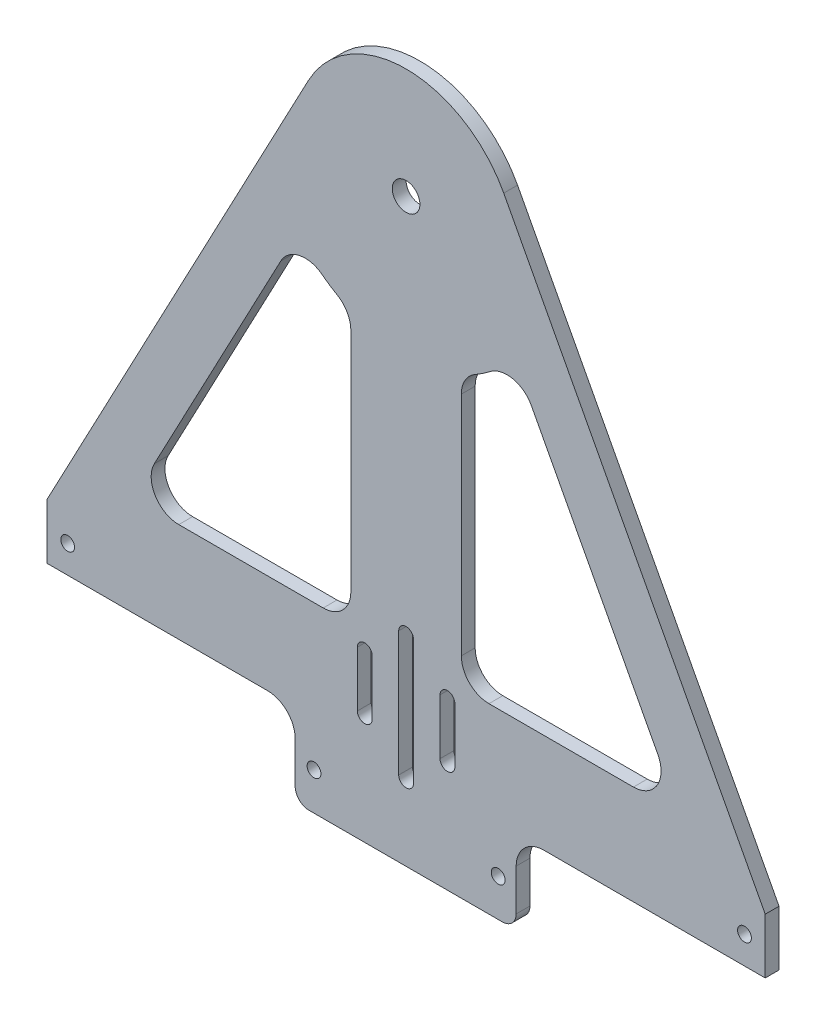
SolidWorks part; units mm, degrees
material "Hexcel AS4C (3000 Filaments)"
ref_plane "Front Plane" through (0, 0, 0) normal (0, 0, 1) x (1, 0, 0)
ref_plane "Top Plane" through (0, 0, 0) normal (0, 1, 0) x (1, 0, 0)
ref_plane "Right Plane" through (0, 0, 0) normal (1, 0, 0) x (0, 0, -1)
sketch "Sketch1" plane through (0, 0, 0) normal (0, 0, 1) x (1, 0, 0)
  line L0 (0, -58.42) -> (0, 58.42) construction
  line L2 (-82.55, 55.7897) -> (-82.55, -52.07)
  line L3 (-76.2, -58.42) -> (76.2, -58.42)
  line L4 (82.55, 55.7897) -> (82.55, -52.07)
  line L5 (-82.55, 58.42) -> (82.55, -58.42) construction
  line L6 (-82.55, -58.42) -> (82.55, 58.42) construction
  line L7 (-80.6901, 60.2799) -> (-75.4296, 65.5404)
  line L8 (-70.9395, 67.4003) -> (-50.8, 67.4003)
  line L9 (-46.3099, 65.5404) -> (-41.0494, 60.2799)
  line L10 (46.3099, 65.5404) -> (41.0494, 60.2799)
  line L11 (70.9395, 67.4003) -> (50.8, 67.4003)
  line L12 (80.6901, 60.2799) -> (75.4296, 65.5404)
  line L13 (-73.5697, 67.4003) -> (-82.55, 67.4003) construction
  line L14 (-82.55, 67.4003) -> (-82.55, 58.42) construction
  line L15 (-36.5592, 58.42) -> (0, 58.42)
  line L16 (0, 58.42) -> (36.5592, 58.42)
  circle A0 centre (-77.7875, -35.052) radius 1.5875
  circle A1 centre (-77.7875, -11.684) radius 1.5875
  circle A2 centre (-77.7875, 11.684) radius 1.5875
  circle A3 centre (-77.7875, 35.052) radius 1.5875
  circle A4 centre (77.7875, 35.052) radius 1.5875
  circle A5 centre (77.7875, 11.684) radius 1.5875
  circle A6 centre (77.7875, -11.684) radius 1.5875
  circle A7 centre (77.7875, -35.052) radius 1.5875
  arc A8 (82.55, 55.7897) -> (80.6901, 60.2799) centre (76.2, 55.7897) ccw
  arc A9 (75.4296, 65.5404) -> (70.9395, 67.4003) centre (70.9395, 61.0503) ccw
  arc A10 (46.3099, 65.5404) -> (50.8, 67.4003) centre (50.8, 61.0503) cw
  arc A11 (41.0494, 60.2799) -> (36.5592, 58.42) centre (36.5592, 64.77) cw
  arc A12 (-36.5592, 58.42) -> (-41.0494, 60.2799) centre (-36.5592, 64.77) cw
  arc A13 (-46.3099, 65.5404) -> (-50.8, 67.4003) centre (-50.8, 61.0503) ccw
  arc A14 (-70.9395, 67.4003) -> (-75.4296, 65.5404) centre (-70.9395, 61.0503) ccw
  arc A15 (-82.55, 55.7897) -> (-80.6901, 60.2799) centre (-76.2, 55.7897) cw
  arc A16 (76.2, -58.42) -> (82.55, -52.07) centre (76.2, -52.07) ccw
  arc A17 (-76.2, -58.42) -> (-82.55, -52.07) centre (-76.2, -52.07) cw
  circle A18 centre (-70.9395, 61.0503) radius 1.5875
  circle A19 centre (-50.8, 61.0503) radius 1.5875
  circle A20 centre (50.8, 61.0503) radius 1.5875
  circle A21 centre (70.9395, 61.0503) radius 1.5875
  point P0 (0, 0)
  point P36 (73.5697, 67.4003)
  point P39 (48.1697, 67.4003)
  point P42 (39.1895, 58.42)
  point P45 (-39.1895, 58.42)
  point P48 (-48.1697, 67.4003)
  dimension "D3" = 3.175
  dimension "D11" = 6.35
  dimension "D12" = 6.35
  dimension "D13" = 3.175
  dimension "D14" = 3.175
  dimension "D1" = 165.1
  dimension "D2" = 116.84
  dimension "D4" = 23.368
  dimension "D5" = 4.7625
  dimension "D7" = 46.736
  dimension "D8" = 12.7
  dimension "D9" = 135
  dimension "D10" = 25.4
  dimension "D6" = 4
extrude "Boss-Extrude1" [suppressed] add sketch "Sketch1" along normal blind 1.5
sketch "Sketch2" [suppressed] plane through (0, 0, 1.5) normal (0, 0, 1) x (1, 0, 0)
  line L0 (0, -45.72) -> (0, 6.3634) construction
  line L1 (0, -58.42) -> (0, 63.5) construction
  line L3 (-82.55, 1.8599) -> (82.55, 1.8599) construction
  line L4 (-82.55, 55.7897) -> (-82.55, -52.07) construction
  line L5 (82.55, -52.07) -> (82.55, 55.7897) construction
  line L7 (-76.2, -58.42) -> (76.2, -58.42) construction
  circle A0 centre (0, -45.72) radius 1.9062
  circle A1 centre (0, 6.3634) radius 1.9062
  dimension "D2" = 3.8125
  dimension "D3" = 3.8125
  dimension "D1" = 52.0834
  dimension "D4" = 12.7
extrude "Cut-Extrude1" [suppressed] cut sketch "Sketch2" against normal through all
sketch "Sketch3" [suppressed] plane through (0, 0, 1.5) normal (0, 0, 1) x (1, 0, 0)
  line L0 (0, 50.8) -> (0, 30.8) construction
  line L1 (-10, 40.8) -> (10, 40.8) construction
  line L2 (-10, 40.8) -> (0, 50.8) construction
  line L3 (0, 50.8) -> (10, 40.8) construction
  line L4 (10, 40.8) -> (0, 30.8) construction
  line L5 (0, 30.8) -> (-10, 40.8) construction
  line L6 (0, 63.5) -> (0, -58.42) construction
  line L8 (-76.2, -58.42) -> (76.2, -58.42) construction
  circle A0 centre (0, 50.8) radius 1.8669
  circle A1 centre (-10, 40.8) radius 1.8669
  circle A2 centre (0, 30.8) radius 1.8669
  circle A3 centre (10, 40.8) radius 1.8669
  dimension "D1" = 3.7338
  dimension "D2" = 12.7
extrude "Cut-Extrude2" [suppressed] cut sketch "Sketch3" against normal through all
sketch "Sketch4" [suppressed] plane through (0, 0, 1.5) normal (0, 0, 1) x (1, 0, 0)
  line L0 (0, 58.42) -> (0, -58.42) construction
  line L1 (36.5592, 58.42) -> (-36.5592, 58.42) construction
  line L2 (-76.2, -58.42) -> (76.2, -58.42) construction
  line L5 (0, 33.045) -> (0, 52.045) construction
  line L6 (-9.5, 42.545) -> (9.5, 42.545) construction
  circle A14 centre (0, 42.545) radius 8 construction
  circle A15 centre (0, 42.545) radius 9.5 construction
  circle A16 centre (0, 50.545) radius 1.5
  circle A17 centre (0, 34.545) radius 1.5
  circle A18 centre (-9.5, 42.545) radius 1.5
  circle A19 centre (9.5, 42.545) radius 1.5
  dimension "D1" = 15.875
  dimension "D3" = 16
  dimension "D4" = 19
  dimension "D5" = 3
  dimension "D6" = 3
  dimension "D7" = 3
  dimension "D8" = 3
extrude "Cut-Extrude3" [suppressed] cut sketch "Sketch4" against normal through all
sketch "Sketch5" plane through (0, 0, 0) normal (0, 0, 1) x (1, 0, 0)
  line L0 (0, 70.8856) -> (0, 39.1356) construction
  line L1 (-82.55, 70.8856) -> (82.55, 70.8856) construction
  line L2 (-82.55, 70.8856) -> (-82.55, 58.1856)
  line L4 (82.55, 70.8856) -> (82.55, 58.1856)
  line L5 (82.55, 70.8856) -> (22.4464, 184.3733)
  line L8 (77.7875, 58.1856) -> (77.7875, 70.8856) construction
  line L11 (0, -48.26) -> (0, -46.3538) construction
  line L12 (0, 70.8856) -> (0, 172.4856) construction
  line L14 (-82.55, 58.1856) -> (-31.849, 58.1856)
  line L15 (-22.324, 39.1356) -> (22.126, 39.1356)
  line L16 (-25.499, 42.3106) -> (-25.499, 51.8356)
  line L17 (25.301, 42.3106) -> (25.301, 51.8356)
  line L18 (31.651, 58.1856) -> (82.55, 58.1856)
  line L19 (-82.55, 70.8856) -> (-22.4464, 184.3733)
  line L20 (-77.7875, 58.1856) -> (-77.7875, 70.8856) construction
  line L23 (0, -0.6801) -> (0, 0) construction
  line L24 (0, 39.1356) -> (0, 70.8856) construction
  line L26 (0, 70.8856) -> (-82.55, 70.8856) construction
  line L27 (-57.8612, 90.3675) -> (-28.8054, 145.2308)
  line L28 (0, -48.26) -> (0, -46.3538) construction
  line L37 (68.1789, 70.8856) -> (11.2232, 178.4295) construction
  line L38 (31.651, 70.8856) -> (68.1789, 70.8856) construction
  line L39 (12.601, 51.8356) -> (12.601, 51.8356) construction
  line L40 (-12.799, 51.8356) -> (12.601, 51.8356) construction
  line L41 (-12.799, 51.8356) -> (-12.799, 51.8356) construction
  line L42 (-68.1789, 70.8856) -> (-31.849, 70.8856) construction
  line L43 (-12.7, 87.3956) -> (-12.7, 139.49)
  line L44 (-68.1789, 70.8856) -> (-11.2232, 178.4295) construction
  line L45 (68.1789, 70.8856) -> (68.1789, 70.8856) construction
  line L46 (-52.2496, 81.0456) -> (-19.05, 81.0456)
  line L47 (-12.7, 70.8856) -> (-12.7, 172.4856) construction
  line L48 (19.05, 81.0456) -> (52.2496, 81.0456) construction
  line L49 (-82.55, 81.0456) -> (82.55, 81.0456) construction
  line L50 (-68.1789, 70.8856) -> (-68.1789, 70.8856) construction
  line L51 (57.8612, 90.3675) -> (28.8054, 145.2308)
  line L52 (52.2496, 81.0456) -> (19.05, 81.0456)
  line L53 (12.7, 87.3956) -> (12.7, 139.49)
  line L54 (-11.2, 64.4741) -> (-11.2, 77.1741)
  line L55 (-7.8, 64.4741) -> (-7.8, 77.1741)
  line L56 (-1.7, 56.4741) -> (-1.7, 85.1741)
  line L57 (1.7, 56.4741) -> (1.7, 85.1741)
  line L58 (7.8, 64.4741) -> (7.8, 77.1741)
  line L59 (11.2, 64.4741) -> (11.2, 77.1741)
  arc A12 (-25.499, 51.8356) -> (-31.849, 58.1856) centre (-31.849, 51.8356) ccw
  arc A13 (25.301, 51.8356) -> (31.651, 58.1856) centre (31.651, 51.8356) cw
  arc A14 (25.301, 42.3106) -> (22.126, 39.1356) centre (22.126, 42.3106) cw
  arc A15 (-25.499, 42.3106) -> (-22.324, 39.1356) centre (-22.324, 42.3106) ccw
  circle A16 centre (-77.7875, 64.5356) radius 1.5875
  circle A17 centre (77.7875, 64.5356) radius 1.5875
  arc A18 (22.4464, 184.3733) -> (-22.4464, 184.3733) centre (0, 172.4856) ccw
  circle A19 centre (0, 172.4856) radius 25.4 construction
  arc A25 (11.2232, 178.4295) -> (-11.2232, 178.4295) centre (0, 172.4856) ccw construction
  arc A26 (12.601, 51.8356) -> (31.651, 70.8856) centre (31.651, 51.8356) cw construction
  arc A27 (-12.799, 51.8356) -> (-31.849, 70.8856) centre (-31.849, 51.8356) ccw construction
  arc A28 (12.601, 51.8356) -> (12.601, 51.8356) centre (12.601, 51.8356) cw construction
  arc A29 (-12.799, 51.8356) -> (-12.799, 51.8356) centre (-12.799, 51.8356) ccw construction
  arc A30 (-19.3282, 147.2966) -> (-15.875, 144.9893) centre (0, 172.4856) ccw
  arc A31 (-19.3282, 147.2966) -> (-28.8054, 145.2308) centre (-23.1938, 142.2588) ccw
  circle A32 centre (0, 172.4856) radius 31.75 construction
  arc A33 (-15.875, 144.9893) -> (-12.7, 139.49) centre (-19.05, 139.49) cw
  arc A34 (-19.05, 81.0456) -> (-12.7, 87.3956) centre (-19.05, 87.3956) ccw
  arc A35 (-52.2496, 81.0456) -> (-57.8612, 90.3675) centre (-52.2496, 87.3956) cw
  arc A36 (15.875, 144.9893) -> (12.7, 139.49) centre (19.05, 139.49) ccw
  arc A37 (19.3282, 147.2966) -> (15.875, 144.9893) centre (0, 172.4856) cw
  arc A38 (19.3282, 147.2966) -> (28.8054, 145.2308) centre (23.1938, 142.2588) cw
  arc A39 (52.2496, 81.0456) -> (57.8612, 90.3675) centre (52.2496, 87.3956) ccw
  arc A40 (19.05, 81.0456) -> (12.7, 87.3956) centre (19.05, 87.3956) cw
  circle A57 centre (0, 64.4741) radius 8 construction
  circle A58 centre (0, 64.4741) radius 9.5 construction
  arc A59 (7.8, 64.4741) -> (11.2, 64.4741) centre (9.5, 64.4741) ccw
  arc A60 (-11.2, 64.4741) -> (-7.8, 64.4741) centre (-9.5, 64.4741) ccw
  arc A62 (-1.7, 56.4741) -> (1.7, 56.4741) centre (0, 56.4741) ccw
  arc A63 (-7.8, 77.1741) -> (-11.2, 77.1741) centre (-9.5, 77.1741) ccw
  arc A64 (11.2, 77.1741) -> (7.8, 77.1741) centre (9.5, 77.1741) ccw
  arc A65 (1.7, 85.1741) -> (-1.7, 85.1741) centre (0, 85.1741) ccw
  circle A66 centre (-21.1667, 47.763) radius 1.5875
  circle A67 centre (21.1667, 47.763) radius 1.5875
  circle A68 centre (0, 172.4856) radius 3.175
  point P0 (0, 0)
  point P52 (25.301, 58.1856)
  point P55 (25.301, 39.1356)
  point P58 (-25.499, 39.1356)
  point P68 (30.3627, 182.0028)
  dimension "D17" = 6.35
  dimension "D18" = 6.35
  dimension "D19" = 3.175
  dimension "D20" = 3.175
  dimension "D21" = 3.175
  dimension "D4" = 50.8
  dimension "D24" = 6.35
  dimension "D25" = 16
  dimension "D26" = 19
  dimension "D27" = 3.4
  dimension "D28" = 3.4
  dimension "D30" = 3.4
  dimension "D31" = 3.4
  dimension "D32" = 3.4
  dimension "D35" = 3.4
  dimension "D36" = 3.175
  dimension "D9" = 6.35
  dimension "D14" = 12.7
  dimension "D15" = 50.8
  dimension "D16" = 19.05
  dimension "D22" = 6.35
  dimension "D3" = 101.6
  dimension "D33" = 12.7
  dimension "D34" = 12.7
  dimension "D8" = 23.1226
  dimension "D10" = 165.1
  dimension "D5" = 12.7
  dimension "D6" = 6.35
  dimension "D7" = 12.7
  dimension "D23" = 10.16
extrude "Boss-Extrude2" add sketch "Sketch5" along normal blind 3.175
equation "\"Top Plate Width\" = 4.5in"
equation "\"Plate Width\" = 3.5in"
equation "\"Plate Thickness\" = 0.375in"
equation "\"Num holes\" = 4"
equation "\"Plate Height\" = 1.25in"
equation "\"Plate Clearance Hole Diameter\" = 0.125in"
equation "\"D3@Sketch1\"=\"Plate Clearance Hole Diameter\""
equation "\"Hole Spacing\"= \"Plate Width\" / ( \"Num holes\" + 1 )"
equation "\"Plate Tap Hole Diameter\" = 0.116in"
equation "\"Bottom Plate Length\" = 6.5in"
equation "\"D21@Sketch5\"=\"Plate Clearance Hole Diameter\""
equation "\"Number Eight Clearance Size\" = 0.177in"
equation "\"Back Brace Height\" = 1.1962912in"
equation "\"Titanium Offset Length\" = 5in"
equation "\"Titanium Head Radius\" = 2in"
equation "\"D4@Sketch5\"=\"Titanium Head Radius\""
equation "\"Titanium Plate Border Thickness\" = 0.5in"
equation "\"D5@Sketch5\"=\"Titanium Plate Border Thickness\""
equation "\"D6@Sketch5\"=\"Titanium Plate Border Thickness\" / 2"
equation "\"D23@Sketch5\"=\"Titanium Plate Border Thickness\"/1.25"
equation "\"slot_hole_length\"=0.75"
